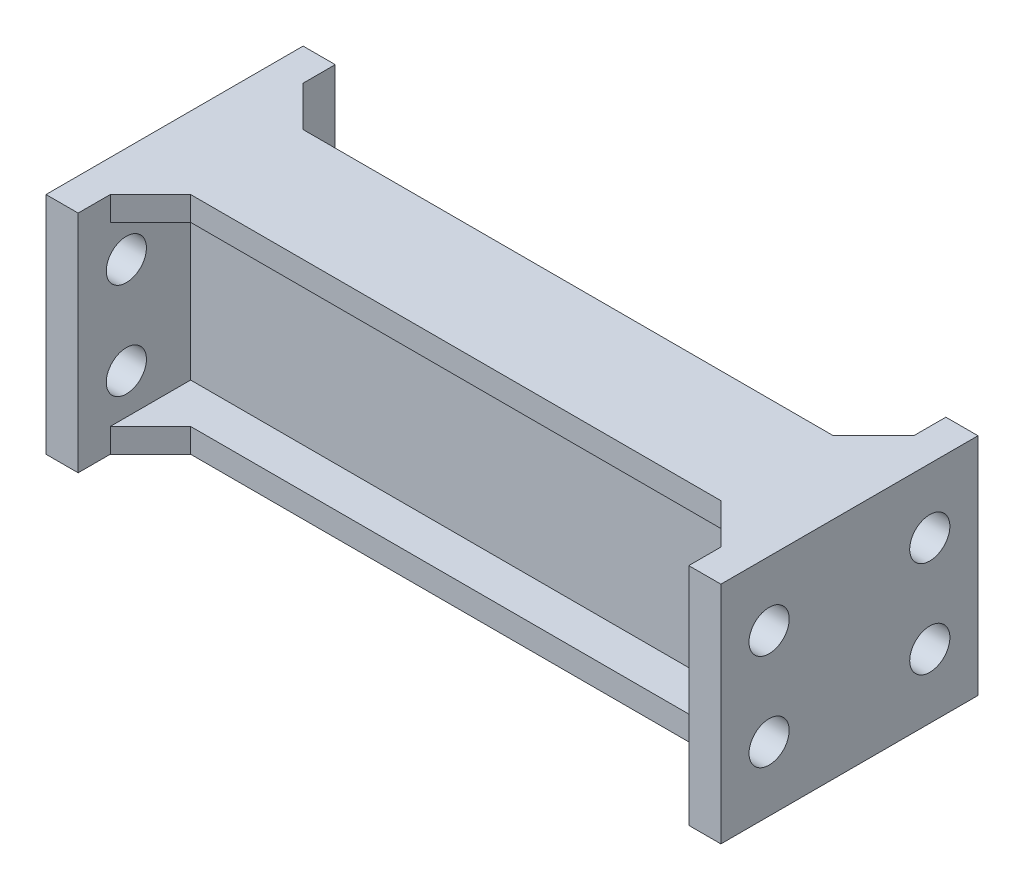
SolidWorks part; units mm, degrees
ref_plane "Front Plane" through (0, 0, 0) normal (0, 0, 1) x (1, 0, 0)
ref_plane "Top Plane" through (0, 0, 0) normal (0, 1, 0) x (1, 0, 0)
ref_plane "Right Plane" through (0, 0, 0) normal (1, 0, 0) x (0, 0, -1)
sketch "Sketch1" plane through (0, 0, 0) normal (0, 1, 0) x (1, 0, 0)
  line L0 (-21, 0) -> (21, 0) construction
  line L1 (-19, 1) -> (19, 1)
  line L2 (-21, 1) -> (-21, -1)
  line L3 (-19, -1) -> (19, -1)
  line L4 (21, 1) -> (21, -1)
  line L5 (-21, 1) -> (21, -1) construction
  line L6 (-21, -1) -> (21, 1) construction
  line L7 (21, 1) -> (21, 8)
  line L8 (19, 1) -> (19, 8)
  line L9 (19, 8) -> (21, 8)
  line L10 (21, -1) -> (21, -8)
  line L11 (19, -8) -> (21, -8)
  line L12 (19, -1) -> (19, -8)
  line L13 (0, 0) -> (0, 1) construction
  line L14 (0, 1) -> (0, -1) construction
  line L15 (-19, -8) -> (-21, -8)
  line L16 (-21, -1) -> (-21, -8)
  line L17 (-19, -1) -> (-19, -8)
  line L18 (-21, 1) -> (-21, 8)
  line L19 (-19, 8) -> (-21, 8)
  line L20 (-19, 1) -> (-19, 8)
  point P0 (0, 0)
  dimension "D1" = 2
  dimension "D2" = 42
  dimension "D3" = 7
  dimension "D4" = 2
extrude "Boss-Extrude1" add sketch "Sketch1" along normal blind 14
sketch "Sketch2" plane through (21, 0, 0) normal (1, 0, 0) x (0, 0, -1)
  line L0 (0, 14) -> (0, 0) construction
  line L1 (-8, 14) -> (8, 14) construction
  line L2 (-8, 7) -> (8, 7) construction
  line L3 (-8, 14) -> (-8, 0) construction
  line L4 (8, 14) -> (8, 0) construction
  circle A0 centre (5, 10) radius 1.25
  circle A1 centre (5, 4) radius 1.25
  circle A2 centre (-5, 4) radius 1.25
  circle A3 centre (-5, 10) radius 1.25
  point P21 (6.5026, 4.0766)
  dimension "D1" = 2.5
  dimension "D2" = 5
  dimension "D3" = 3
extrude "Cut-Extrude1" cut sketch "Sketch2" against normal through all
sketch "Sketch3" plane through (0, 14, 0) normal (0, 1, 0) x (1, 0, 0)
  line L0 (-19, 1) -> (-19, 6)
  line L1 (-19, 1) -> (-19, 8) construction
  line L2 (-19, 1) -> (-14, 1)
  line L3 (19, 1) -> (-19, 1) construction
  line L4 (-19, 6) -> (-16.5, 3.5)
  line L5 (-21, 0) -> (21, 0) construction
  line L6 (-21, 8) -> (-21, -8) construction
  line L7 (21, -8) -> (21, 8) construction
  line L8 (0, 1) -> (0, -1) construction
  line L9 (-19, -1) -> (19, -1) construction
  line L10 (19, 1) -> (19, 6)
  line L11 (19, 1) -> (14, 1)
  line L12 (19, 6) -> (16.5, 3.5)
  line L13 (19, -1) -> (14, -1)
  line L14 (19, -6) -> (16.5, -3.5)
  line L15 (19, -1) -> (19, -6)
  line L16 (-19, -1) -> (-19, -6)
  line L17 (-19, -1) -> (-14, -1)
  line L18 (-19, -6) -> (-16.5, -3.5)
  line L19 (-16.5, 3.5) -> (16.5, 3.5)
  line L20 (-14, 1) -> (14, 1)
  line L21 (-16.5, -3.5) -> (16.5, -3.5)
  line L22 (-14, -1) -> (14, -1)
  dimension "D1" = 5
  dimension "D2" = 5
extrude "Boss-Extrude2" add sketch "Sketch3" against normal blind 1.5
ref_plane "Plane1" through (0, 7, 0) normal (0, 1, 0) x (1, 0, 0)
mirror "Mirror1" about plane through (0, 7, 0) normal (0, 1, 0) of "Boss-Extrude2"
